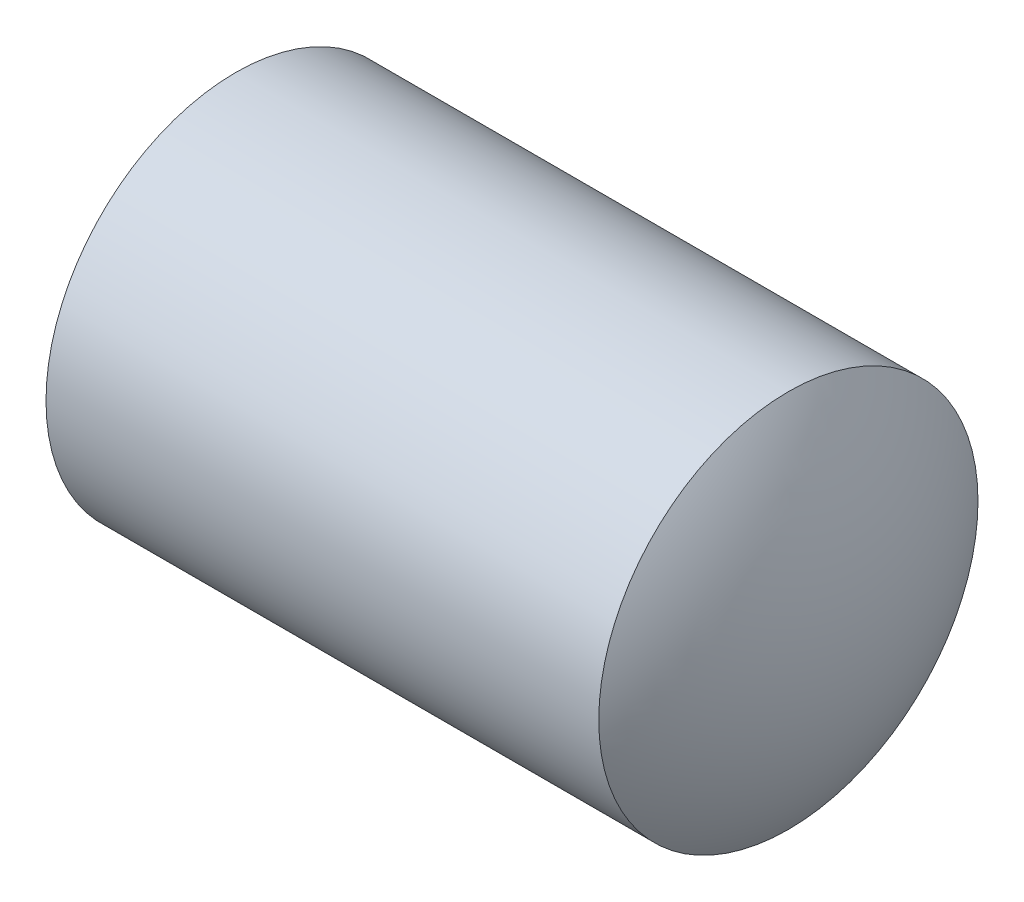
SolidWorks part; units mm, degrees
revolve "BaseBody" add sketch "BodySke" angle 360 about L5
sketch "BodySke" plane through (0, 0, 0) normal (0, 0, 1) x (1, 0, 0)
  line L0 (0, 0) -> (0, 1.2195)
  line L1 (0, 1.2195) -> (0.1619, 1.5)
  line L2 (0.1619, 1.5) -> (4.5346, 1.5)
  line L3 (0.5, 15.875) -> (0.5, -3.175) construction
  line L4 (5, 0) -> (0, 0)
  line L5 (-12.7, 0) -> (88.9, 0) construction
  line L8 (0, -1.2195) -> (0.1619, -1.5) construction
  arc A0 (5, 0) -> (4.5346, 1.5) centre (2.35, 0) ccw
  dimension "Oval_radius" = 2.65
  dimension "Diameter" = 3
  dimension "Drive_ch_ang" = 60
  dimension "Minor_dia" = 2.439
  dimension "Length" = 5
  dimension "Advance" = 0.5
cosmetic thread "ThreadCosmetic" parameters "Thread_minor"=2.439
ref_plane "Plane1" through (0, 0, 0) normal (0, 0, 1) x (1, 0, 0)
ref_plane "Plane2" through (0, 0, 0) normal (0, 1, 0) x (1, 0, 0)
ref_plane "Plane3" through (0, 0, 0) normal (1, 0, 0) x (0, 0, -1)
sketch "Sketch2" plane through (0, 0, 0) normal (-1, 0, 0) x (0, 0, 1)
  line L0 (0.433, 0.75) -> (-0.433, 0.75)
  line L1 (-0.433, 0.75) -> (-0.866, 0)
  line L2 (0.433, 0.75) -> (0.866, 0)
  line L3 (0.433, -0.75) -> (0.866, 0)
  line L4 (0.433, -0.75) -> (-0.433, -0.75)
  line L5 (-0.433, -0.75) -> (-0.866, 0)
  dimension "Hex_size" = 1.5
  dimension "D2" = 0.75
  dimension "D3" = 0.75
extrude "Hex" cut sketch "Sketch2" against normal blind 2.1
sketch "Sketch4" plane through (0, 4.7709, -0.5249) normal (-1, 0, 0) x (0, 0, 1)
  line L0 (0.5249, -4.7709) -> (1.3124, -4.7709)
  line L1 (0.5249, -4.7709) -> (6.6732, -1.2211) construction
  line L2 (0.5249, -4.7709) -> (0.9186, -4.0889)
  line L3 (1.153, -4.6137) -> (1.2782, -4.5415)
  line L4 (0.975, -4.3054) -> (1.1002, -4.2332)
  arc A0 (1.153, -4.6137) -> (0.975, -4.3054) centre (0.5249, -4.7709) ccw
  arc A1 (1.3124, -4.7709) -> (1.2782, -4.5415) centre (0.5249, -4.7709) ccw
  arc A2 (0.9186, -4.0889) -> (1.1002, -4.2332) centre (0.5249, -4.7709) cw
  circle A3 centre (0.5249, -4.7709) radius 0.6475 construction
  circle A4 centre (0.5249, -4.7709) radius 0.7875 construction
  dimension "Spline_n_dim" = 1.295
  dimension "Spline_m_dim" = 1.575
  dimension "D1" = 30
  dimension "Spline_a_dim" = 60
  dimension "Spline_p_dim" = 0.356
  dimension "D3" = 0.178
extrude "Spline6" [suppressed] cut sketch "Sketch4" against normal blind 1.2
pattern_circular "CirPattern1" [suppressed] count 6 every 60 about axis through (-12.7, 0, 0) along (1, 0, 0)
sketch "Sketch5" plane through (0, -2.3417, -0.7053) normal (-1, 0, 0) x (0, 0, 1)
  line L0 (0.7053, 2.3417) -> (1.4928, 2.3417)
  line L1 (0.7053, 2.3417) -> (5.7254, 7.3618) construction
  line L2 (0.7053, 2.3417) -> (0.7053, 3.1292)
  line L3 (1.289, 2.6736) -> (1.3736, 2.7582)
  line L4 (1.0373, 2.9254) -> (1.1218, 3.01)
  line L5 (1.0373, 2.9254) -> (1.289, 2.6736)
  arc A1 (1.4928, 2.3417) -> (1.3736, 2.7582) centre (0.7053, 2.3417) ccw
  arc A2 (0.7053, 3.1292) -> (1.1218, 3.01) centre (0.7053, 2.3417) cw
  circle A3 centre (0.7053, 2.3417) radius 0.6475 construction
  circle A4 centre (0.7053, 2.3417) radius 0.7875 construction
  dimension "Spline_n_dim" = 1.295
  dimension "Spline_m_dim" = 1.575
  dimension "Spline_p_dim" = 0.356
  dimension "D3" = 0.178
  dimension "D1" = 45
  dimension "Spline_a_dim" = 90
extrude "Spline4" [suppressed] cut sketch "Sketch5" against normal blind 1.2
pattern_circular "CirPattern2" [suppressed] count 4 every 90 about axis through (-12.7, 0, 0) along (1, 0, 0)
sketch "ThdSchSke" plane through (0, 0, 0) normal (0, 0, 1) x (1, 0, 0)
  line L0 (0.1619, -1.2195) -> (-0.0345, -1.5)
  line L1 (0.1619, -1.2195) -> (0.3584, -1.5)
  line L2 (0.3584, -1.5) -> (0.3584, -1.875)
  line L3 (-3.175, 0) -> (5.1513, 0) construction
  line L4 (0.1619, 1.5) -> (0.1619, -1.5) construction
  line L5 (0.3584, -1.875) -> (-0.0345, -1.875)
  line L6 (-0.0345, -1.875) -> (-0.0345, -1.5)
  dimension "Thread_minor" = 2.439
  dimension "Diameter" = 3
revolve "ThreadSchematic" [suppressed] cut sketch "ThdSchSke" angle 360 about L3
pattern_linear "ThdSchPat" [suppressed]
equation "\"D2@Sketch2\" = \"Hex_size@Sketch2\" / 2"
equation "\"D3@Sketch2\" = \"Hex_size@Sketch2\" / 2"
equation "\"Thread_minor@ThreadCosmetic\" = \"Minor_dia@BodySke\""
equation "\"D1@Sketch4\" = \"Spline_a_dim@Sketch4\" / 2"
equation "\"D3@Sketch4\" = \"Spline_p_dim@Sketch4\" / 2"
equation "\"D2@CirPattern1\" = \"Spline_a_dim@Sketch4\""
equation "\"Num_teeth@CirPattern1\" = 360 / \"D2@CirPattern1\""
equation "\"Spline_a_dim@Sketch5\" = 90"
equation "\"Spline_p_dim@Sketch5\" = \"Spline_p_dim@Sketch4\""
equation "\"Spline_m_dim@Sketch5\" = \"Spline_m_dim@Sketch4\""
equation "\"Spline_n_dim@Sketch5\" = \"Spline_n_dim@Sketch4\""
equation "\"D1@Sketch5\" = \"Spline_a_dim@Sketch5\" / 2"
equation "\"D3@Sketch5\" = \"Spline_p_dim@Sketch5\" / 2"
equation "\"Key_eng@Spline4\" = \"Key_eng@Spline6\""
equation "\"Thread_minor@ThdSchSke\" = \"Thread_minor@ThreadCosmetic\""
equation "\"Diameter@ThdSchSke\" = \"Diameter@BodySke\""
equation "\"Overcut@ThdSchSke\" = \"Diameter@BodySke\" * 1.25"
equation "\"Num_threads@ThdSchPat\" = int( (\"Length@BodySke\" - ( ( ( \"Diameter@BodySke\" - \"Minor_dia@BodySke\" ) * 0.5 ) / tan( \"Drive_ch_ang@BodySke\" * 0.017453292 ) ) - ( \"Oval_radius@BodySke\" - sqr ( ( \"Oval_radius@BodySke\" * \"Oval_radius@BodySke\" ) - ( ( \"Diameter@BodySke\" * 0.5 ) * ( \"Diameter@BodySke\" * 0.5 ) ) ) ) ) / \"Advance@BodySke\" + 0.999 )  + 1"
equation "\"Advance@ThdSchPat\" = (\"Length@BodySke\" - ( ( ( \"Diameter@BodySke\" - \"Minor_dia@BodySke\" ) * 0.5 ) / tan( \"Drive_ch_ang@BodySke\" * 0.017453292 ) ) - ( \"Oval_radius@BodySke\" - sqr ( ( \"Oval_radius@BodySke\" * \"Oval_radius@BodySke\" ) - ( ( \"Diameter@BodySke\" * 0.5 ) * ( \"Diameter@BodySke\" * 0.5 ) ) ) ) ) /  (\"Num_threads@ThdSchPat\" - 1) 'relax it"
equation "' \"Num_threads@ThdSchPat\" = \"Num_threads@ThdSchPat\" - sgn( \"Num_threads@ThdSchPat\" - 1) '---chamfered tips only---"
